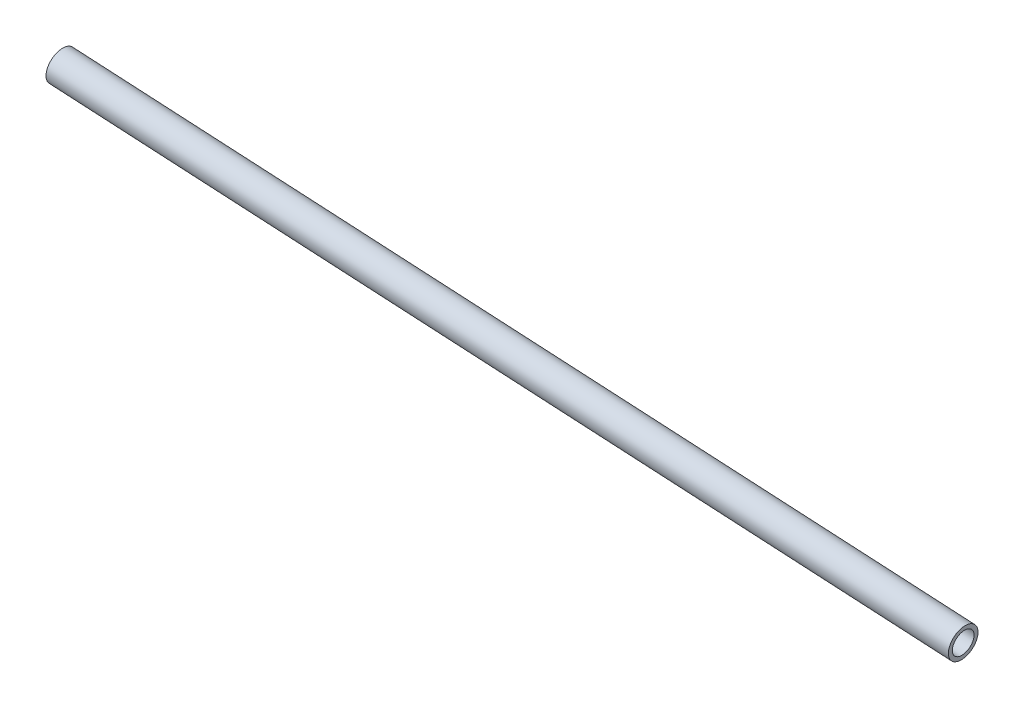
SolidWorks part; units mm, degrees
ref_plane "Front Plane" through (0, 0, 0) normal (0, 0, 1) x (1, 0, 0)
ref_plane "Top Plane" through (0, 0, 0) normal (0, 1, 0) x (1, 0, 0)
ref_plane "Right Plane" through (0, 0, 0) normal (1, 0, 0) x (0, 0, -1)
sketch3d "reference sketch"
  line L1 (192.7225, -0.198, -0.1143) -> (737.4634, -48.71, -43.4913) construction
  line L6 (762.8634, -48.7102, -43.4911) -> (737.4634, -48.71, -43.4913)
  line L7 (711.4298, 39.261, -58.896) -> (763.6157, -137.3594, -75.4897)
  line L8 (762.1115, 39.9438, -62.2925) -> (711.4298, 39.261, -58.896)
  line L9 (763.6157, -137.3594, -75.4897) -> (762.1115, 39.9438, -62.2925)
  line L11 (762.8636, -48.7078, -68.8911) -> (762.8634, -48.7102, -43.4911)
sketch3d "3DSketch2"
  line L0 (192.7225, -0.198, -0.1143) -> (737.4632, -48.7125, -18.0911)
  line L1 (762.8636, -48.7078, -68.8911) -> (762.8632, -48.7125, -18.0911) construction
  line L2 (762.8636, -48.7078, -68.8911) -> (762.8634, -48.7102, -43.4911) construction
  line L3 (762.8632, -48.7125, -18.0911) -> (737.4632, -48.7125, -18.0911) construction
  point P4 (737.4632, -48.7125, -18.0911)
  point P5 (192.7225, -0.198, -0.1143)
  dimension "D1" = 25.4
  dimension "D2" = 25.4
other "Pipe standard s40 PIPE 1 SCH 40(1)"
ref_plane "Plane1" through (192.7225, -0.198, -0.1143) normal (0.9955, -0.0887, -0.0329) x (-0.0247, 0.0913, -0.9955)
sketch "Sketch1" plane through (192.7225, -0.198, -0.1143) normal (0.9955, -0.0887, -0.0329) x (-0.0247, 0.0913, -0.9955)
  circle A0 centre (0, 0) radius 6.985
  circle A1 centre (0, 0) radius 9.525
  point P3 (0, 0)
  dimension "Out_dia" = 19.05
  dimension "D1" = 2.54
